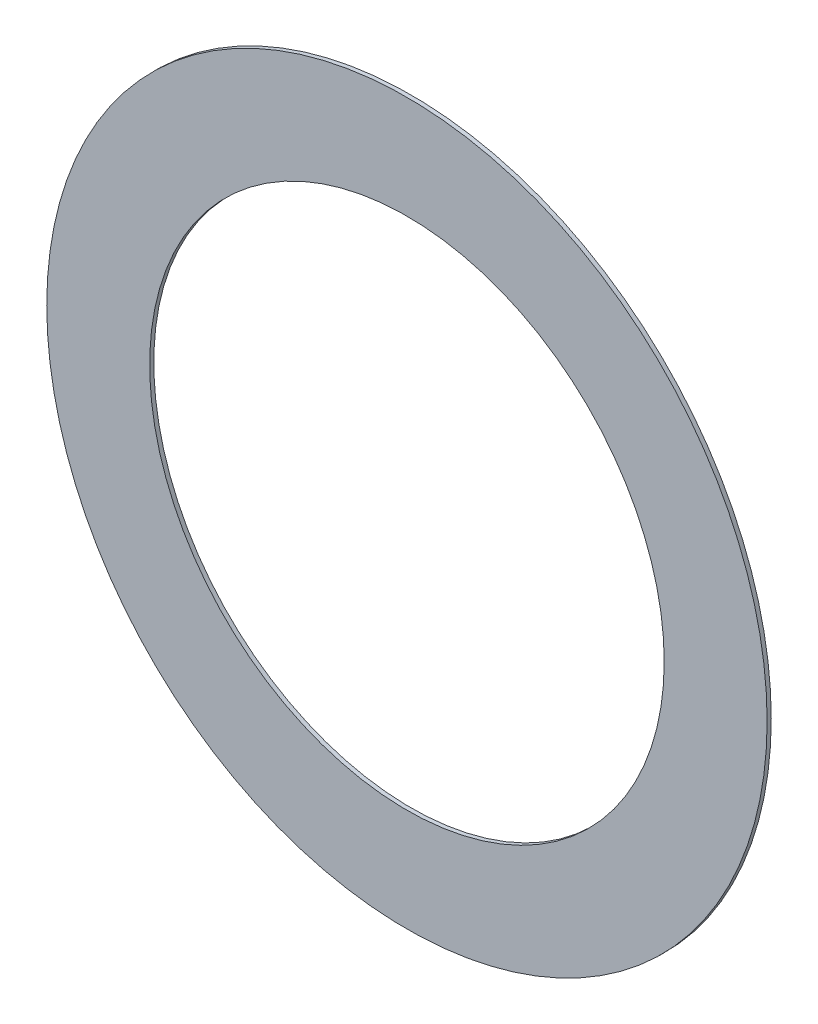
SolidWorks part; units mm, degrees
material "AISI 1020"
ref_plane "Front Plane" through (0, 0, 0) normal (0, 0, 1) x (1, 0, 0)
ref_plane "Top Plane" through (0, 0, 0) normal (0, 1, 0) x (1, 0, 0)
ref_plane "Right Plane" through (0, 0, 0) normal (1, 0, 0) x (0, 0, -1)
sketch "Sketch1" plane through (0, 0, 0) normal (0, 0, 1) x (1, 0, 0)
  circle A0 centre (0, 0) radius 15.875
  circle A1 centre (0, 0) radius 22.225
  dimension "D1" = 31.75
  dimension "D2" = 44.45
extrude "Boss-Extrude1" add sketch "Sketch1" along normal blind 0.254
